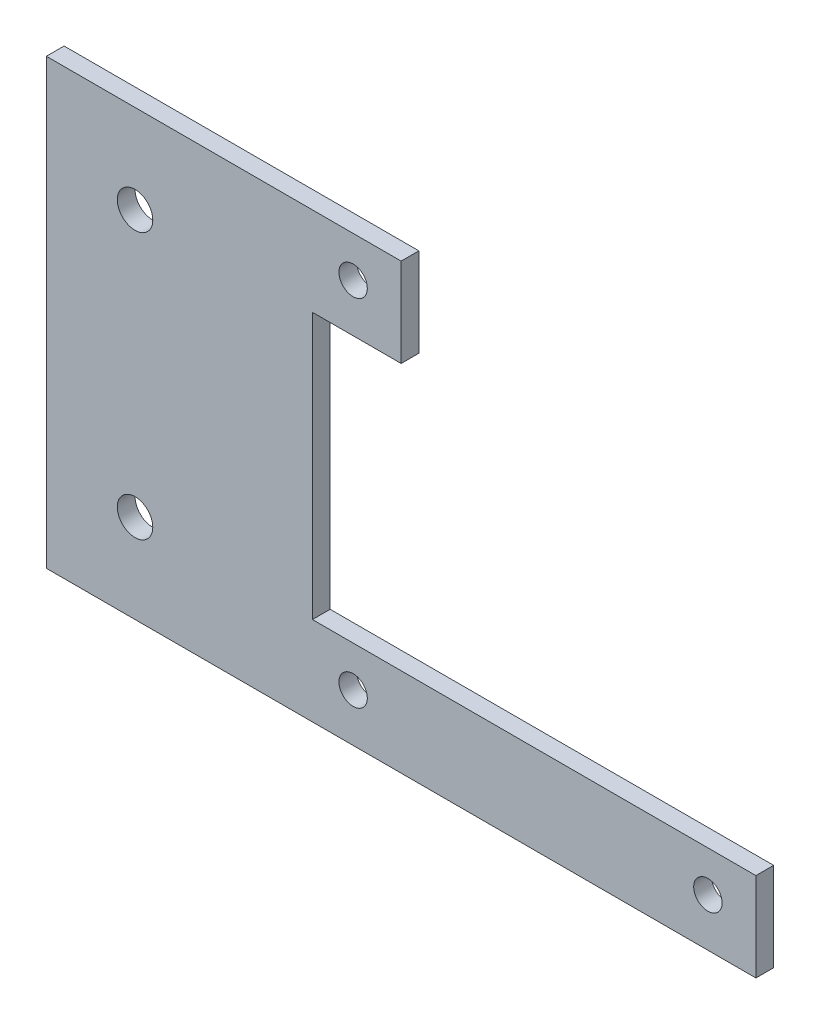
SolidWorks part; units mm, degrees
ref_plane "Ön Düzlem" through (0, 0, 0) normal (0, 0, 1) x (1, 0, 0)
ref_plane "Üst Düzlem" through (0, 0, 0) normal (0, 1, 0) x (1, 0, 0)
ref_plane "Sağ Düzlem" through (0, 0, 0) normal (1, 0, 0) x (0, 0, -1)
sketch "Sketch2" plane through (0, 0, 0) normal (0, 0, 1) x (1, 0, 0)
  line L0 (-10, -34.9441) -> (-10, -84.9441)
  line L1 (-10, -220) -> (-10, 0) construction
  line L3 (-10, -84.9441) -> (70, -84.9441)
  line L4 (70, -84.9441) -> (70, -74.9441)
  line L5 (70, -74.9441) -> (20, -74.9441)
  line L6 (30, -44.9441) -> (20, -44.9441)
  line L7 (20, -74.9441) -> (20, -44.9441)
  line L8 (30, -44.9441) -> (30, -34.9441)
  line L9 (30, -34.9441) -> (-10, -34.9441)
  line L11 (24.5872, -39.5312) -> (64.5872, -39.5312) construction
  line L12 (24.5872, -39.5312) -> (24.5872, -79.5312) construction
  line L13 (24.5872, -79.5312) -> (64.5872, -79.5312) construction
  line L14 (64.5872, -39.5312) -> (64.5872, -79.5312) construction
  line L15 (24.5872, -39.5312) -> (64.5872, -79.5312) construction
  line L16 (24.5872, -79.5312) -> (64.5872, -39.5312) construction
  circle A0 centre (24.5872, -39.5312) radius 1.6
  circle A1 centre (24.5872, -79.5312) radius 1.6
  circle A2 centre (64.5872, -79.5312) radius 1.6
  circle A3 centre (0, -74.9441) radius 2
  circle A4 centre (0, -44.9441) radius 2
  point P4 (44.5872, -59.5312)
  point P24 (0.8455, -34.9441)
  dimension "D7" = 3.2
  dimension "D8" = 4
  dimension "D1" = 50
  dimension "D2" = 30
  dimension "D3" = 40
  dimension "D4" = 10
  dimension "D5" = 10
  dimension "D6" = 50
  dimension "D9" = 10
  dimension "D10" = 10
  dimension "D11" = 10
extrude "Boss-Extrude1" add sketch "Sketch2" along normal blind 2
